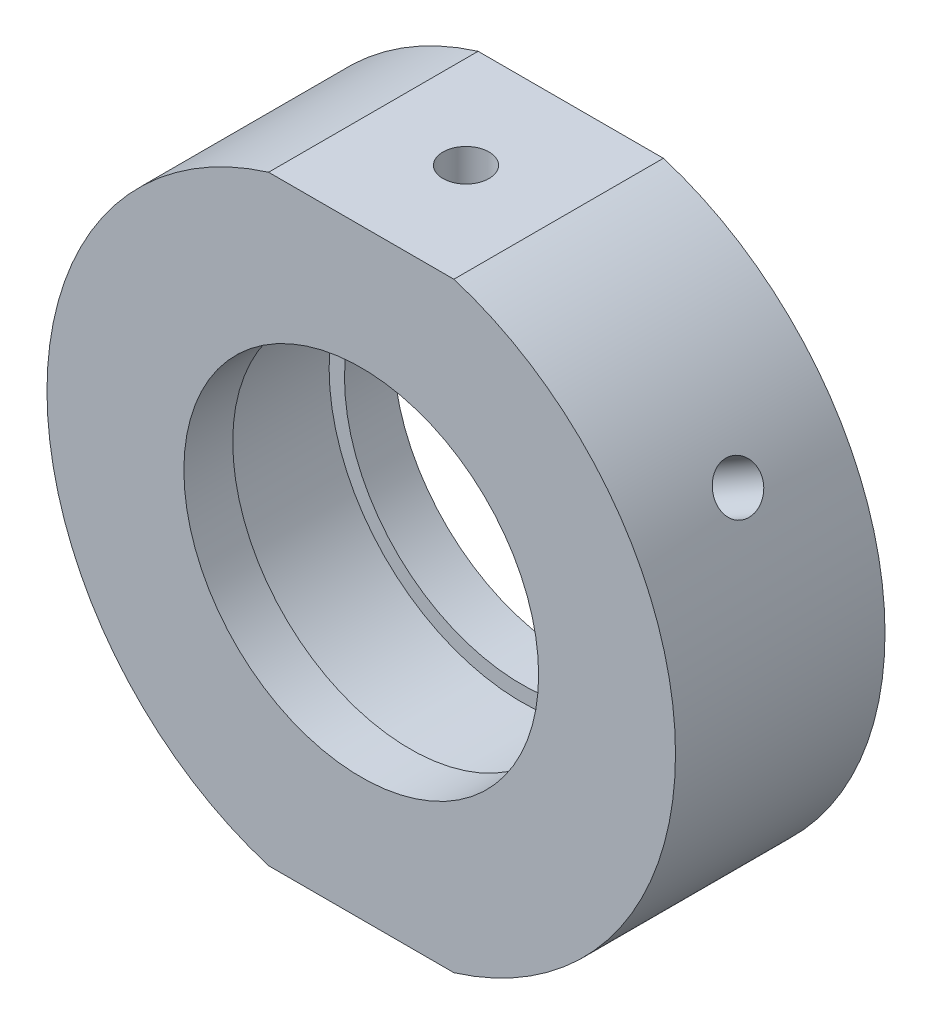
SolidWorks part; units mm, degrees
ref_plane "前视基准面" through (0, 0, 0) normal (0, 0, 1) x (1, 0, 0)
ref_plane "上视基准面" through (0, 0, 0) normal (0, 1, 0) x (1, 0, 0)
ref_plane "右视基准面" through (0, 0, 0) normal (1, 0, 0) x (0, 0, -1)
sketch "草图1" plane through (0, 0, 0) normal (0, 1, 0) x (1, 0, 0)
  line L0 (0, 31.9391) -> (0, -26.491) construction
  line L1 (22.5, 7.5) -> (22.5, -7.5)
  line L6 (22.5, -7.5) -> (12.7, -7.5)
  line L7 (12.7, -7.5) -> (12.7, -4)
  line L8 (12.7, -4) -> (13.8, -4)
  line L9 (13.8, -4) -> (13.8, 4)
  line L10 (13.8, 4) -> (12.7, 4)
  line L11 (12.7, 4) -> (12.7, 7.5)
  line L12 (12.7, 7.5) -> (22.5, 7.5)
  line L17 (19.05, 0) -> (-5.0345, 0) construction
  point P6 (13.8, 0)
  dimension "D2" = 13.8
  dimension "D3" = 12.7
  dimension "D4" = 12.7
  dimension "D5" = 15
  dimension "D6" = 3.5
  dimension "D7" = 7.5
  dimension "D9" = 22.5
  dimension "D14" = 8
  dimension "D15" = 4
  dimension "D18" = 0
revolve "旋转1" add sketch "草图1" angle 360 about L0
sketch "草图2" plane through (0, 0, 7.5) normal (0, 0, 1) x (1, 0, 0)
  line L0 (0, 0) -> (43.1523, 0) construction
  line L1 (-33.152, 30.7489) -> (30.8698, 30.7489)
  line L2 (-33.152, 30.7489) -> (-33.152, 21.5)
  line L3 (-33.152, 21.5) -> (30.8698, 21.5)
  line L4 (30.8698, 30.7489) -> (30.8698, 21.5)
  line L5 (30.8698, -30.7489) -> (30.8698, -21.5)
  line L6 (-33.152, -21.5) -> (30.8698, -21.5)
  line L7 (-33.152, -30.7489) -> (-33.152, -21.5)
  line L8 (-33.152, -30.7489) -> (30.8698, -30.7489)
  dimension "D1" = 21.5
extrude "切除-拉伸1" cut sketch "草图2" against normal blind 49
sketch "草图10" plane through (0, 0, 0) normal (0, 0, 1) x (1, 0, 0)
  line L0 (0, 21.5) -> (0, -21.5)
  line L1 (-6.6332, 21.5) -> (6.6332, 21.5) construction
  line L2 (-6.6332, -21.5) -> (6.6332, -21.5) construction
  line L3 (0, 0) -> (-19.4856, 11.25)
  line L4 (0, 0) -> (19.4856, 11.25)
  arc A2 (6.6332, -21.5) -> (6.6332, 21.5) centre (0, 0) ccw construction
  arc A3 (-6.6332, 21.5) -> (-6.6332, -21.5) centre (0, 0) ccw construction
  arc A4 (19.4856, 11.25) -> (6.6332, 21.5) centre (0, 0) ccw
  arc A5 (-6.6332, 21.5) -> (-19.4856, 11.25) centre (0, 0) ccw
  dimension "D1" = 60
  dimension "D2" = 60
hole_wizard "M4 螺纹孔2" positions "草图15" profile "草图16" tap size "M4" standard "ISO"
sketch "草图15" plane through (0, 21.5, 0) normal (0, 1, 0) x (1, 0, 0)
  point P0 (0, 0)
sketch "草图16" plane through (0, 21.5, 0) normal (1, 0, 0) x (0, 0, 1)
  line L0 (0, 0) -> (0, 6.4914)
  line L1 (0, 6.4914) -> (1.65, 5.5)
  line L2 (1.65, 5.5) -> (1.65, 0)
  line L5 (1.65, 0) -> (0, 0)
  line L10 (0, 6.4914) -> (-1.65, 5.5) construction
  line L11 (0, -6.35) -> (0, 107.95) construction
  dimension "螺纹孔钻头直径" = 3.3
  dimension "螺纹孔钻头深度" = 5.5
  dimension "导头角度" = 118
cosmetic thread "孔螺蚊线1"
hole_wizard "M6 螺纹孔2" positions "草图17" profile "草图18" tap size "M6" standard "ISO"
sketch "草图17" plane through (0, -21.5, 0) normal (0, -1, 0) x (-1, 0, 0)
  point P0 (0, 0)
sketch "草图18" plane through (0, -21.5, 0) normal (1, 0, 0) x (0, 0, -1)
  line L0 (0, 0) -> (0, 7.0022)
  line L1 (0, 7.0022) -> (2.5, 5.5)
  line L2 (2.5, 5.5) -> (2.5, 0)
  line L5 (2.5, 0) -> (0, 0)
  line L10 (0, 7.0022) -> (-2.5, 5.5) construction
  line L11 (0, -6.35) -> (0, 107.95) construction
  dimension "螺纹孔钻头直径" = 5
  dimension "螺纹孔钻头深度" = 5.5
  dimension "导头角度" = 118
cosmetic thread "孔螺蚊线2" parameters "D1"=5.5, "D2"=6
hole_wizard "M4 螺纹孔3" positions "3D草图4" profile "草图22" tap size "M4" standard "ISO"
sketch3d "3D草图4"
  point P0 (-19.4856, 11.25, 0)
  point P4 (19.4856, 11.25, 0)
  point P7 (19.4856, 11.25, 0)
  point P11 (-19.4856, 11.25, 0)
  point P15 (19.4856, 11.25, 0)
  point P17 (19.4856, 11.25, 0)
sketch "草图22" plane through (19.4856, 11.25, 0) normal (0, 0, 1) x (-0.5, 0.866, 0)
  line L0 (0, 0) -> (0, 14.3914)
  line L1 (0, 14.3914) -> (1.65, 13.4)
  line L2 (1.65, 13.4) -> (1.65, 0)
  line L5 (1.65, 0) -> (0, 0)
  line L10 (0, 14.3914) -> (-1.65, 13.4) construction
  line L11 (0, -6.35) -> (0, 107.95) construction
  dimension "螺纹孔钻头直径" = 3.3
  dimension "螺纹孔钻头深度" = 13.4
  dimension "导头角度" = 118
cosmetic thread "孔螺蚊线4"
cosmetic thread "孔螺蚊线5"
